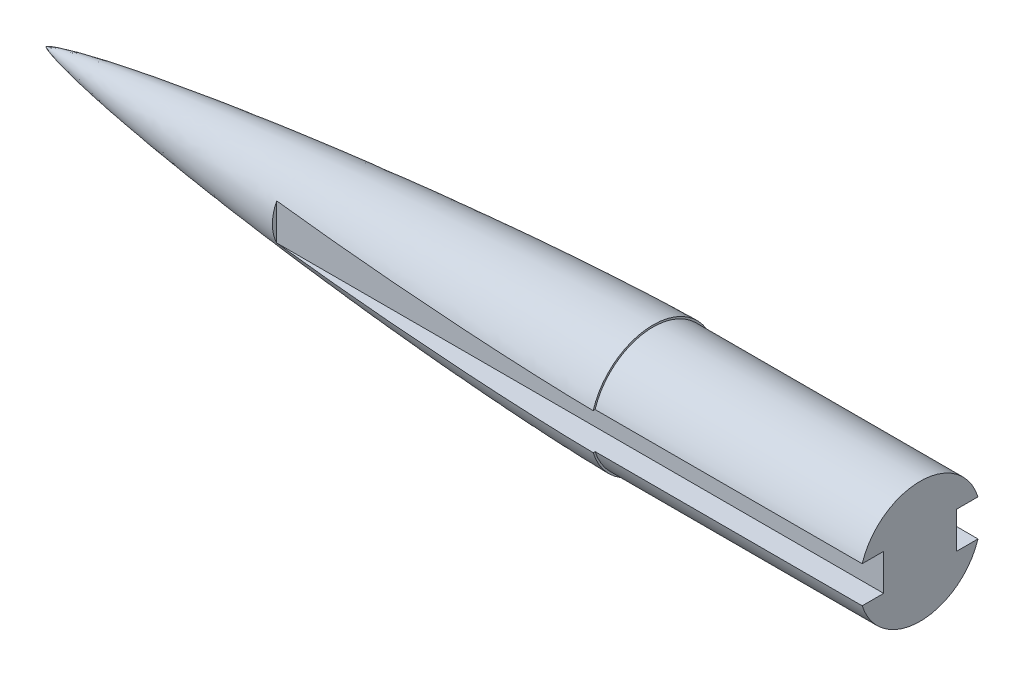
SolidWorks part; units mm, degrees
ref_plane "Front Plane" through (0, 0, 0) normal (0, 0, 1) x (1, 0, 0)
ref_plane "Top Plane" through (0, 0, 0) normal (0, 1, 0) x (1, 0, 0)
ref_plane "Right Plane" through (0, 0, 0) normal (1, 0, 0) x (0, 0, -1)
sketch "Sketch1" plane through (0, 0, 0) normal (0, 0, 1) x (1, 0, 0)
  line L0 (0, 0) -> (685.8, 0)
  line L1 (55.2447, 0) -> (-55.2447, 0) construction
  line L2 (685.8, 63.5) -> (635, 63.5)
  line L3 (635, 63.5) -> (635, 65.405)
  line L4 (685.8, 63.5) -> (685.8, 0)
  spline S0 degree 4 poles (0, 0) (0.0022, 0.0063) (0.0075, 0.0184) (0.0223, 0.0404) (0.057, 0.0804) (0.1098, 0.1304) (0.1816, 0.1889) (0.2836, 0.2634) (0.4063, 0.3444) (0.5502, 0.4318) (0.7155, 0.5251) (0.9567, 0.6537) (1.3318, 0.8391) (1.9703, 1.1275) (3.1158, 1.5922) (5.1634, 2.3284) (8.9332, 3.5155) (16.022, 5.4463) (28.2617, 8.305) (49.1788, 12.5136) (77.9573, 17.4873) (112.8708, 22.8061) (151.8575, 28.1242) (190.9036, 32.9827) (229.9952, 37.4592) (269.1232, 41.6038) (308.2821, 45.4454) (347.4678, 49.0026) (386.6776, 52.2836) (425.9094, 55.2895) (465.1619, 58.0128) (504.4341, 60.4362) (538.8141, 62.2665) (568.2945, 63.5925) (591.9899, 64.4666) (607.8766, 64.942) (620.8678, 65.2384) (628.9431, 65.3608) (632.981, 65.3999) (635, 65.405) knots 0 0 0 0 0 0.000041 0.000083 0.000165 0.000331 0.000496 0.000661 0.000955 0.001249 0.001549 0.001849 0.002664 0.003866 0.00593 0.009578 0.01627 0.028579 0.051871 0.088176 0.149698 0.211221 0.272743 0.334265 0.395788 0.45731 0.518832 0.580355 0.641877 0.703399 0.764922 0.826444 0.887966 0.918727 0.949489 0.974744 0.987372 1 1 1 1 1 construction
  spline S1 degree 4 poles (0, 0) (0.0022, 0.0063) (0.0075, 0.0184) (0.0223, 0.0404) (0.057, 0.0804) (0.1098, 0.1304) (0.1816, 0.1889) (0.2836, 0.2634) (0.4063, 0.3444) (0.5502, 0.4318) (0.7155, 0.5251) (0.9567, 0.6537) (1.3318, 0.8391) (1.9703, 1.1275) (3.1158, 1.5922) (5.1634, 2.3284) (8.9332, 3.5155) (16.022, 5.4463) (28.2617, 8.305) (49.1788, 12.5136) (77.9573, 17.4873) (112.8708, 22.8061) (151.8575, 28.1242) (190.9036, 32.9827) (229.9952, 37.4592) (269.1232, 41.6038) (308.2821, 45.4454) (347.4678, 49.0026) (386.6776, 52.2836) (425.9094, 55.2895) (465.1619, 58.0128) (504.4341, 60.4362) (538.8141, 62.2665) (568.2945, 63.5925) (591.9899, 64.4666) (607.8766, 64.942) (620.8678, 65.2384) (628.9431, 65.3608) (632.981, 65.3999) (635, 65.405) knots 0 0 0 0 0 0.000041 0.000083 0.000165 0.000331 0.000496 0.000661 0.000955 0.001249 0.001549 0.001849 0.002664 0.003866 0.00593 0.009578 0.01627 0.028579 0.051871 0.088176 0.149698 0.211221 0.272743 0.334265 0.395788 0.45731 0.518832 0.580355 0.641877 0.703399 0.764922 0.826444 0.887966 0.918727 0.949489 0.974744 0.987372 1 1 1 1 1
  dimension "D1" = 635
  dimension "D2" = 50.8
  dimension "D3" = 63.5
  dimension "D4" = 65.405
revolve "Revolve1" add sketch "Sketch1" angle 360 about L0
sketch "Sketch2" plane through (685.8, 0, 0) normal (1, 0, 0) x (0, 0, -1)
  line L0 (-38.1, 19.05) -> (-38.1, -19.05)
  line L1 (-76.2, 19.05) -> (76.2, 19.05)
  line L2 (-76.2, 19.05) -> (-76.2, -19.05)
  line L3 (-76.2, -19.05) -> (76.2, -19.05)
  line L4 (76.2, 19.05) -> (76.2, -19.05)
  line L5 (-76.2, 19.05) -> (76.2, -19.05) construction
  line L6 (-76.2, -19.05) -> (76.2, 19.05) construction
  line L8 (-76.2, -18.415) -> (-76.2, 18.415)
  line L10 (76.2, -18.415) -> (76.2, 18.415)
  line L11 (-76.2, -18.415) -> (76.2, 18.415) construction
  line L12 (-76.2, 18.415) -> (76.2, -18.415) construction
  line L13 (0, 19.05) -> (38.1, 19.05)
  line L14 (0, 19.05) -> (0, -19.05)
  line L15 (0, -19.05) -> (38.1, -19.05)
  line L16 (38.1, 19.05) -> (38.1, -19.05)
  circle A0 centre (0, 0) radius 65.405 construction
  circle A1 centre (0, 0) radius 65.405
  point P0 (0, 0)
  point P6 (0, 0)
  circle M4 centre (0, 0) radius 63.5
  dimension "D1" = 38.1
  dimension "D2" = 152.4
  dimension "D3" = 38.1
extrude "Cut-Extrude1" cut sketch "Sketch2" against normal blind 406.4 contours A1 L3 L4 L1 | L3 A1 L1 M4 | A1 L1 L2 L3 | L1 A1 L3 M4 | L3 L0 L1 M4 | L1 L16 L3 M4
sketch "Sketch5" plane through (685.8, 0, 0) normal (1, 0, 0) x (0, 0, -1)
  line L6 (-38.1, 19.05) -> (-38.1, -19.05)
  line L7 (-38.1, -19.05) -> (-60.5751, -19.05)
  line L8 (60.5751, -19.05) -> (38.1, -19.05)
  line L9 (38.1, -19.05) -> (38.1, 19.05)
  line L10 (38.1, 19.05) -> (60.5751, 19.05)
  line L11 (-60.5751, 19.05) -> (-38.1, 19.05)
  line L12 (-38.1, 19.05) -> (-38.1, -19.05)
  line L13 (-38.1, -19.05) -> (-60.5751, -19.05)
  line L14 (60.5751, -19.05) -> (38.1, -19.05)
  line L15 (38.1, -19.05) -> (38.1, 19.05)
  line L16 (38.1, 19.05) -> (60.5751, 19.05)
  line L17 (-60.5751, 19.05) -> (-38.1, 19.05)
  arc A2 (-60.5751, -19.05) -> (60.5751, -19.05) centre (0, 0) ccw
  arc A3 (60.5751, 19.05) -> (-60.5751, 19.05) centre (0, 0) ccw
  arc A4 (-60.5751, -19.05) -> (60.5751, -19.05) centre (0, 0) ccw
  arc A5 (60.5751, 19.05) -> (-60.5751, 19.05) centre (0, 0) ccw
  line M9 (-38.1, 19.05) -> (-38.1, -19.05)
  line M10 (-38.1, -19.05) -> (-60.5751, -19.05)
  arc M11 (-60.5751, -19.05) -> (60.5751, -19.05) centre (0, 0) ccw
  line M12 (60.5751, -19.05) -> (38.1, -19.05)
  line M13 (38.1, -19.05) -> (38.1, 19.05)
  line M14 (38.1, 19.05) -> (60.5751, 19.05)
  arc M15 (60.5751, 19.05) -> (-60.5751, 19.05) centre (0, 0) ccw
  line M16 (-60.5751, 19.05) -> (-38.1, 19.05)
  dimension "D1" = 0
extrude "Boss-Extrude2" add sketch "Sketch5" along normal blind 228.6 contours M16 M9 M10 M11 M12 M13 M14 M15
equation "\"D_o\"= 5.15in"
equation "\"D_i\"= 5in"
equation "\"D_c\"= 4.8in"
equation "\"L\"= 25in"
equation "\"L_s\"= 2in"
equation "\"D2@Sketch1\"=\"L_s\""
equation "\"D1@Sketch1\"=\"L\""
equation "\"D3@Sketch1\"=\"D_i\"/2"
equation "\"D4@Sketch1\"=\"D_o\"/2"
